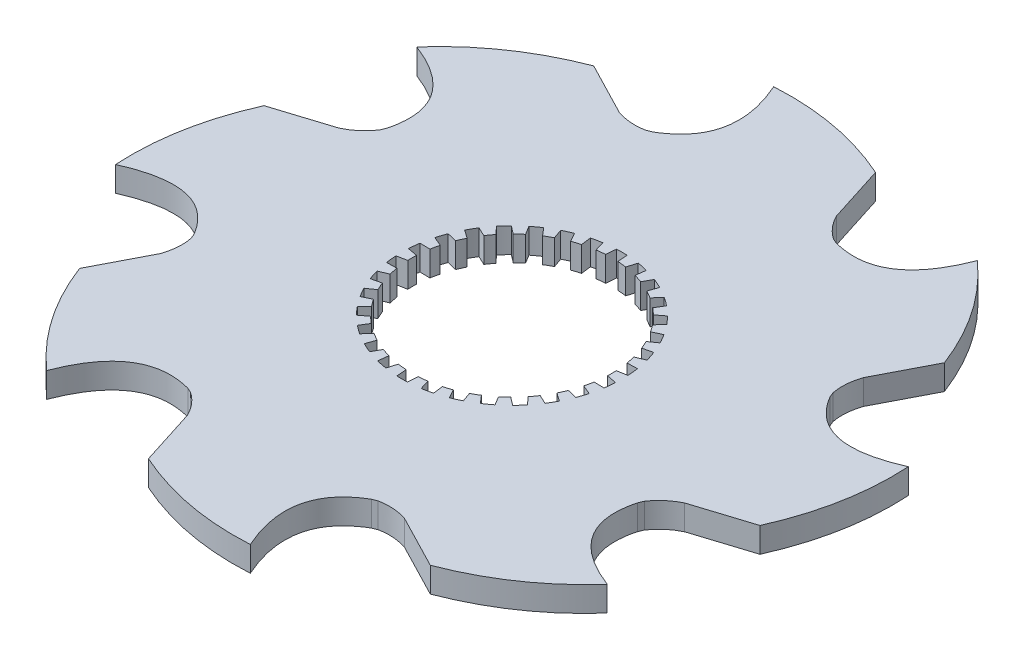
SolidWorks part; units mm, degrees
ref_plane "Front Plane" through (0, 0, 0) normal (0, 0, 1) x (1, 0, 0)
ref_plane "Top Plane" through (0, 0, 0) normal (0, 1, 0) x (1, 0, 0)
ref_plane "Right Plane" through (0, 0, 0) normal (1, 0, 0) x (0, 0, -1)
sketch "Sketch1" plane through (0, 0, 0) normal (0, 1, 0) x (1, 0, 0)
  line L0 (16.0828, 52.6433) -> (12.2342, 64.7462)
  line L1 (48.5967, 25.8522) -> (54.4334, 37.1315)
  line L2 (52.6433, -16.0828) -> (64.7462, -12.2342)
  line L3 (25.8522, -48.5967) -> (37.1315, -54.4334)
  line L4 (-16.0828, -52.6433) -> (-12.2342, -64.7462)
  line L5 (-48.5967, -25.8522) -> (-54.4334, -37.1315)
  line L6 (-52.6433, 16.0828) -> (-64.7462, 12.2342)
  line L7 (-25.8522, 48.5967) -> (-37.1315, 54.4334)
  arc A1 (-18.8238, 48.5484) -> (-19.8207, 48.15) centre (0, 0) ccw
  arc A2 (-47.6394, 21.0185) -> (-48.0625, 20.0319) centre (0, 0) ccw
  arc A3 (-48.5484, -18.8238) -> (-48.15, -19.8207) centre (0, 0) ccw
  arc A4 (-21.0185, -47.6394) -> (-20.0319, -48.0625) centre (0, 0) ccw
  arc A5 (18.8238, -48.5484) -> (19.8207, -48.15) centre (0, 0) ccw
  arc A6 (47.6394, -21.0185) -> (48.0625, -20.0319) centre (0, 0) ccw
  arc A7 (48.5484, 18.8238) -> (48.15, 19.8207) centre (0, 0) ccw
  arc A8 (21.0185, 47.6394) -> (20.0319, 48.0625) centre (0, 0) ccw
  spline S0 degree 2 poles (16.0828, 52.6433) (17.4582, 49.8018) (20.0319, 48.0625) knots 0 0 0 1 1 1
  spline S1 degree 2 poles (12.2342, 64.7462) (-0.6325, 70.4856) (-14.26, 69.6757) knots 0 0 0 1 1 1
  spline S2 degree 2 poles (-14.26, 69.6757) (-7.6888, 54.9743) (-18.8238, 48.5484) knots 0 0 0 1 1 1
  spline S3 degree 2 poles (39.1849, 59.3515) (33.4359, 44.3095) (21.0185, 47.6394) knots 0 0 0 1 1 1
  spline S4 degree 2 poles (54.4334, 37.1315) (49.3937, 50.2881) (39.1849, 59.3515) knots 0 0 0 1 1 1
  spline S5 degree 2 poles (48.5967, 25.8522) (47.5599, 22.8704) (48.15, 19.8207) knots 0 0 0 1 1 1
  spline S6 degree 2 poles (69.6757, 14.26) (54.9743, 7.6888) (48.5484, 18.8238) knots 0 0 0 1 1 1
  spline S7 degree 2 poles (64.7462, -12.2342) (70.4856, 0.6325) (69.6757, 14.26) knots 0 0 0 1 1 1
  spline S8 degree 2 poles (52.6433, -16.0828) (49.8018, -17.4582) (48.0625, -20.0319) knots 0 0 0 1 1 1
  spline S9 degree 2 poles (59.3515, -39.1849) (44.3095, -33.4359) (47.6394, -21.0185) knots 0 0 0 1 1 1
  spline S10 degree 2 poles (37.1315, -54.4334) (50.2881, -49.3937) (59.3515, -39.1849) knots 0 0 0 1 1 1
  spline S11 degree 2 poles (25.8522, -48.5967) (22.8704, -47.5599) (19.8207, -48.15) knots 0 0 0 1 1 1
  spline S12 degree 2 poles (14.26, -69.6757) (7.6888, -54.9743) (18.8238, -48.5484) knots 0 0 0 1 1 1
  spline S13 degree 2 poles (-12.2342, -64.7462) (0.6325, -70.4856) (14.26, -69.6757) knots 0 0 0 1 1 1
  spline S14 degree 2 poles (-16.0828, -52.6433) (-17.4582, -49.8018) (-20.0319, -48.0625) knots 0 0 0 1 1 1
  spline S15 degree 2 poles (-39.1849, -59.3515) (-33.4359, -44.3095) (-21.0185, -47.6394) knots 0 0 0 1 1 1
  spline S16 degree 2 poles (-54.4334, -37.1315) (-49.3937, -50.2881) (-39.1849, -59.3515) knots 0 0 0 1 1 1
  spline S17 degree 2 poles (-48.5967, -25.8522) (-47.5599, -22.8704) (-48.15, -19.8207) knots 0 0 0 1 1 1
  spline S18 degree 2 poles (-69.6757, -14.26) (-54.9743, -7.6888) (-48.5484, -18.8238) knots 0 0 0 1 1 1
  spline S19 degree 2 poles (-64.7462, 12.2342) (-70.4856, -0.6325) (-69.6757, -14.26) knots 0 0 0 1 1 1
  spline S20 degree 2 poles (-52.6433, 16.0828) (-49.8018, 17.4582) (-48.0625, 20.0319) knots 0 0 0 1 1 1
  spline S21 degree 2 poles (-59.3515, 39.1849) (-44.3095, 33.4359) (-47.6394, 21.0185) knots 0 0 0 1 1 1
  spline S22 degree 2 poles (-37.1315, 54.4334) (-50.2881, 49.3937) (-59.3515, 39.1849) knots 0 0 0 1 1 1
  spline S23 degree 2 poles (-25.8522, 48.5967) (-22.8704, 47.5599) (-19.8207, 48.15) knots 0 0 0 1 1 1
  point P70 (0, 0)
  dimension "D1" = 8
  dimension "D2" = 12
extrude "Boss-Extrude3" add sketch "Sketch1" along normal blind 5.2917 contours L7 S22 S21 A2 S20 L6 S19 S18 A3 S17 L5 S16 S15 A4 S14 L4 S13 S12 A5 S11 L3 S10 S9 A6 S8 L2 S7 S6 A7 S5 L1 S4 S3 A8 S0 L0 S1 S2 A1 S23
sketch "Sketch6" plane through (0, 5.2917, 0) normal (0, 1, 0) x (1, 0, 0)
  point P0 (0, 0)
scale "Scale1" scale about centroid uniform scaling yes scale factor 0.6
sketch "Sketch9" plane through (0, 4.2333, 0) normal (0, 1, 0) x (1, 0, 0)
  line L1 (0.6703, 13.9539) -> (0.7753, 12.6763)
  line L2 (-0.6703, 13.9539) -> (-0.7753, 12.6763)
  line L3 (2.2456, 13.7883) -> (1.8772, 12.5605)
  line L4 (3.5568, 13.5096) -> (3.3939, 12.2381)
  line L5 (5.0633, 13.0201) -> (4.4476, 11.8957)
  line L6 (6.2879, 12.4749) -> (5.8642, 11.265)
  line L7 (7.6597, 11.6829) -> (6.8237, 10.7111)
  line L8 (8.7442, 10.895) -> (8.0782, 9.7996)
  line L9 (9.9213, 9.8351) -> (8.9015, 9.0583)
  line L10 (10.8183, 8.8389) -> (9.9391, 7.9059)
  line L11 (11.7493, 7.5574) -> (10.5903, 7.0096)
  line L12 (12.4196, 6.3965) -> (11.3657, 5.6667)
  line L13 (13.0638, 4.9494) -> (11.8163, 4.6546)
  line L14 (13.4781, 3.6745) -> (12.2955, 3.1798)
  line L15 (13.8074, 2.1252) -> (12.5258, 2.0961)
  line L16 (13.9475, 0.792) -> (12.6879, 0.554)
  line L17 (13.9475, -0.792) -> (12.6879, -0.554)
  line L18 (13.8074, -2.1252) -> (12.5258, -2.0961)
  line L19 (13.4781, -3.6745) -> (12.2955, -3.1798)
  line L20 (13.0638, -4.9494) -> (11.8163, -4.6546)
  line L21 (12.4196, -6.3965) -> (11.3657, -5.6667)
  line L22 (11.7493, -7.5574) -> (10.5903, -7.0096)
  line L23 (10.8183, -8.8389) -> (9.9391, -7.9059)
  line L24 (9.9213, -9.8351) -> (8.9015, -9.0583)
  line L25 (8.7442, -10.895) -> (8.0782, -9.7996)
  line L26 (7.6597, -11.6829) -> (6.8237, -10.7111)
  line L27 (6.2879, -12.4749) -> (5.8642, -11.265)
  line L28 (5.0633, -13.0201) -> (4.4476, -11.8957)
  line L29 (3.5568, -13.5096) -> (3.3939, -12.2381)
  line L30 (2.2456, -13.7883) -> (1.8772, -12.5605)
  line L31 (0.6703, -13.9539) -> (0.7753, -12.6763)
  line L32 (-0.6703, -13.9539) -> (-0.7753, -12.6763)
  line L33 (-2.2456, -13.7883) -> (-1.8772, -12.5605)
  line L34 (-3.5568, -13.5096) -> (-3.3939, -12.2381)
  line L35 (-5.0633, -13.0201) -> (-4.4476, -11.8957)
  line L36 (-6.2879, -12.4749) -> (-5.8642, -11.265)
  line L37 (-7.6597, -11.6829) -> (-6.8237, -10.7111)
  line L38 (-8.7442, -10.895) -> (-8.0782, -9.7996)
  line L39 (-9.9213, -9.8351) -> (-8.9015, -9.0583)
  line L40 (-10.8183, -8.8389) -> (-9.9391, -7.9059)
  line L41 (-11.7493, -7.5574) -> (-10.5903, -7.0096)
  line L42 (-12.4196, -6.3965) -> (-11.3657, -5.6667)
  line L43 (-13.0638, -4.9494) -> (-11.8163, -4.6546)
  line L44 (-13.4781, -3.6745) -> (-12.2955, -3.1798)
  line L45 (-13.8074, -2.1252) -> (-12.5258, -2.0961)
  line L46 (-13.9475, -0.792) -> (-12.6879, -0.554)
  line L47 (-13.9475, 0.792) -> (-12.6879, 0.554)
  line L48 (-13.8074, 2.1252) -> (-12.5258, 2.0961)
  line L49 (-13.4781, 3.6745) -> (-12.2955, 3.1798)
  line L50 (-13.0638, 4.9494) -> (-11.8163, 4.6546)
  line L51 (-12.4196, 6.3965) -> (-11.3657, 5.6667)
  line L52 (-11.7493, 7.5574) -> (-10.5903, 7.0096)
  line L53 (-10.8183, 8.8389) -> (-9.9391, 7.9059)
  line L54 (-9.9213, 9.8351) -> (-8.9015, 9.0583)
  line L55 (-8.7442, 10.895) -> (-8.0782, 9.7996)
  line L56 (-7.6597, 11.6829) -> (-6.8237, 10.7111)
  line L57 (-6.2879, 12.4749) -> (-5.8642, 11.265)
  line L58 (-5.0633, 13.0201) -> (-4.4476, 11.8957)
  line L59 (-3.5568, 13.5096) -> (-3.3939, 12.2381)
  line L60 (-2.2456, 13.7883) -> (-1.8772, 12.5605)
  arc A0 (-0.7753, 12.6763) -> (-1.8772, 12.5605) centre (0, 0) ccw
  arc A1 (-2.2456, 13.7883) -> (-3.5568, 13.5096) centre (0, 0) ccw
  arc A2 (-3.3939, 12.2381) -> (-4.4476, 11.8957) centre (0, 0) ccw
  arc A3 (0.6703, 13.9539) -> (-0.6703, 13.9539) centre (0, 0) ccw
  arc A4 (-5.0633, 13.0201) -> (-6.2879, 12.4749) centre (0, 0) ccw
  arc A5 (-5.8642, 11.265) -> (-6.8237, 10.7111) centre (0, 0) ccw
  arc A6 (-7.6597, 11.6829) -> (-8.7442, 10.895) centre (0, 0) ccw
  arc A7 (-8.0782, 9.7996) -> (-8.9015, 9.0583) centre (0, 0) ccw
  arc A8 (-9.9213, 9.8351) -> (-10.8183, 8.8389) centre (0, 0) ccw
  arc A9 (-9.9391, 7.9059) -> (-10.5903, 7.0096) centre (0, 0) ccw
  arc A10 (-11.7493, 7.5574) -> (-12.4196, 6.3965) centre (0, 0) ccw
  arc A11 (-11.3657, 5.6667) -> (-11.8163, 4.6546) centre (0, 0) ccw
  arc A12 (-13.0638, 4.9494) -> (-13.4781, 3.6745) centre (0, 0) ccw
  arc A13 (-12.2955, 3.1798) -> (-12.5258, 2.0961) centre (0, 0) ccw
  arc A14 (-13.8074, 2.1252) -> (-13.9475, 0.792) centre (0, 0) ccw
  arc A15 (-12.6879, 0.554) -> (-12.6879, -0.554) centre (0, 0) ccw
  arc A16 (-13.9475, -0.792) -> (-13.8074, -2.1252) centre (0, 0) ccw
  arc A17 (-12.5258, -2.0961) -> (-12.2955, -3.1798) centre (0, 0) ccw
  arc A18 (-13.4781, -3.6745) -> (-13.0638, -4.9494) centre (0, 0) ccw
  arc A19 (-11.8163, -4.6546) -> (-11.3657, -5.6667) centre (0, 0) ccw
  arc A20 (-12.4196, -6.3965) -> (-11.7493, -7.5574) centre (0, 0) ccw
  arc A21 (-10.5903, -7.0096) -> (-9.9391, -7.9059) centre (0, 0) ccw
  arc A22 (-10.8183, -8.8389) -> (-9.9213, -9.8351) centre (0, 0) ccw
  arc A23 (-8.9015, -9.0583) -> (-8.0782, -9.7996) centre (0, 0) ccw
  arc A24 (-8.7442, -10.895) -> (-7.6597, -11.6829) centre (0, 0) ccw
  arc A25 (-6.8237, -10.7111) -> (-5.8642, -11.265) centre (0, 0) ccw
  arc A26 (-6.2879, -12.4749) -> (-5.0633, -13.0201) centre (0, 0) ccw
  arc A27 (-4.4476, -11.8957) -> (-3.3939, -12.2381) centre (0, 0) ccw
  arc A28 (-3.5568, -13.5096) -> (-2.2456, -13.7883) centre (0, 0) ccw
  arc A29 (-1.8772, -12.5605) -> (-0.7753, -12.6763) centre (0, 0) ccw
  arc A30 (-0.6703, -13.9539) -> (0.6703, -13.9539) centre (0, 0) ccw
  arc A31 (0.7753, -12.6763) -> (1.8772, -12.5605) centre (0, 0) ccw
  arc A32 (2.2456, -13.7883) -> (3.5568, -13.5096) centre (0, 0) ccw
  arc A33 (3.3939, -12.2381) -> (4.4476, -11.8957) centre (0, 0) ccw
  arc A34 (5.0633, -13.0201) -> (6.2879, -12.4749) centre (0, 0) ccw
  arc A35 (5.8642, -11.265) -> (6.8237, -10.7111) centre (0, 0) ccw
  arc A36 (8.0782, -9.7996) -> (8.9015, -9.0583) centre (0, 0) ccw
  arc A37 (9.9213, -9.8351) -> (10.8183, -8.8389) centre (0, 0) ccw
  arc A38 (7.6597, -11.6829) -> (8.7442, -10.895) centre (0, 0) ccw
  arc A39 (9.9391, -7.9059) -> (10.5903, -7.0096) centre (0, 0) ccw
  arc A40 (11.7493, -7.5574) -> (12.4196, -6.3965) centre (0, 0) ccw
  arc A41 (11.3657, -5.6667) -> (11.8163, -4.6546) centre (0, 0) ccw
  arc A42 (13.0638, -4.9494) -> (13.4781, -3.6745) centre (0, 0) ccw
  arc A43 (12.2955, -3.1798) -> (12.5258, -2.0961) centre (0, 0) ccw
  arc A44 (13.8074, -2.1252) -> (13.9475, -0.792) centre (0, 0) ccw
  arc A45 (12.6879, -0.554) -> (12.6879, 0.554) centre (0, 0) ccw
  arc A46 (13.9475, 0.792) -> (13.8074, 2.1252) centre (0, 0) ccw
  arc A47 (12.5258, 2.0961) -> (12.2955, 3.1798) centre (0, 0) ccw
  arc A48 (13.4781, 3.6745) -> (13.0638, 4.9494) centre (0, 0) ccw
  arc A49 (11.8163, 4.6546) -> (11.3657, 5.6667) centre (0, 0) ccw
  arc A50 (12.4196, 6.3965) -> (11.7493, 7.5574) centre (0, 0) ccw
  arc A51 (10.5903, 7.0096) -> (9.9391, 7.9059) centre (0, 0) ccw
  arc A52 (10.8183, 8.8389) -> (9.9213, 9.8351) centre (0, 0) ccw
  arc A53 (8.9015, 9.0583) -> (8.0782, 9.7996) centre (0, 0) ccw
  arc A54 (8.7442, 10.895) -> (7.6597, 11.6829) centre (0, 0) ccw
  arc A55 (6.8237, 10.7111) -> (5.8642, 11.265) centre (0, 0) ccw
  arc A56 (6.2879, 12.4749) -> (5.0633, 13.0201) centre (0, 0) ccw
  arc A57 (4.4476, 11.8957) -> (3.3939, 12.2381) centre (0, 0) ccw
  arc A58 (3.5568, 13.5096) -> (2.2456, 13.7883) centre (0, 0) ccw
  arc A59 (1.8772, 12.5605) -> (0.7753, 12.6763) centre (0, 0) ccw
  point P130 (0, 0)
extrude "Cut-Extrude1" cut sketch "Sketch9" against normal through all contours A8 L53 A9 L52 A10 L51 A11 L50 A12 L49 A13 L48 A14 L47 A15 L46 A16 L45 A17 L44 A18 L43 A19 L42 A20 L41 A21 L40 A22 L39 A23 L38 A24 L37 A25 L36 A26 L35 A27 L34 A28 L33 A29 L32 A30 L31 A31 L30 A32 L29 A33 L28 A34 L27 A35 L26 A38 L25 A36 L24 A37 L23 A39 L22 A40 L21 A41 L20 A42 L19 A43 L18 A44 L17 A45 L16 A46 L15 A47 L14 A48 L13 A49 L12 A50 L11 A51 L10 A52 L9 A53 L8 A54 L7 A55 L6 A56 L5 A57 L4 A58 L3 A59 L1 A3 L2 A0 L60 A1 L59 A2 L58 A4 L57 A5 L56 A6 L55 A7 L54
